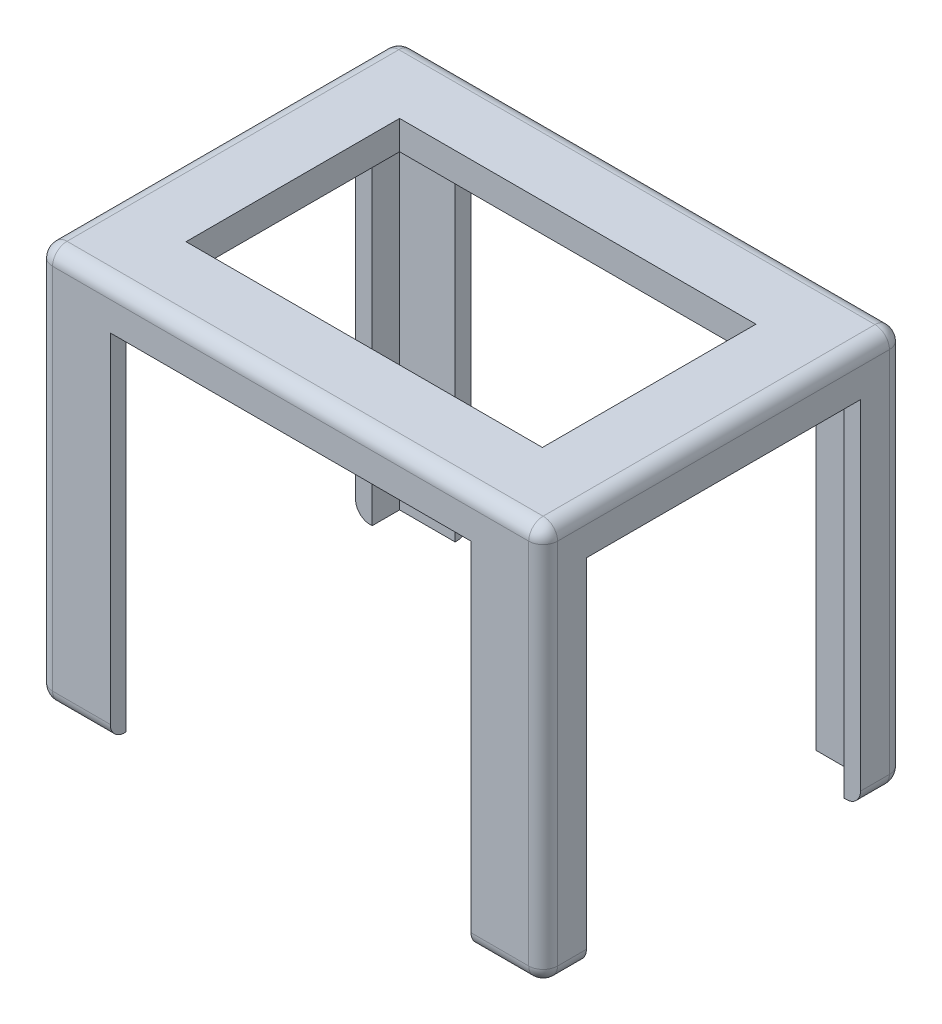
SolidWorks part; units mm, degrees
ref_plane "Front Plane" through (0, 0, 0) normal (0, 0, 1) x (1, 0, 0)
ref_plane "Top Plane" through (0, 0, 0) normal (0, 1, 0) x (1, 0, 0)
ref_plane "Right Plane" through (0, 0, 0) normal (1, 0, 0) x (0, 0, -1)
sketch "Sketch1" plane through (0, 0, 0) normal (0, 1, 0) x (1, 0, 0)
  line L1 (0, 0) -> (88.9, 0)
  line L2 (0, 0) -> (0, -63.5)
  line L3 (0, -63.5) -> (88.9, -63.5)
  line L4 (88.9, 0) -> (88.9, -63.5)
  dimension "D1" = 88.9
  dimension "D2" = 63.5
extrude "Boss-Extrude2" add sketch "Sketch1" along normal blind 69.85
fillet "Fillet2" radius 2.54 12 edges at (0, 69.85, 31.75) (0, 0, 31.75) (44.45, 69.85, 0) (0, 34.925, 0) (44.45, 0, 0) (88.9, 69.85, 31.75) (88.9, 34.925, 0) (88.9, 0, 31.75) (0, 34.925, 63.5) (44.45, 69.85, 63.5) (88.9, 34.925, 63.5) (44.45, 0, 63.5)
sketch "Sketch3" plane through (0, 69.85, 0) normal (0, 1, 0) x (1, 0, 0)
  line L0 (0, -2.54) -> (0, -60.96) construction
  line L1 (2.921, -2.794) -> (85.979, -2.794)
  line L2 (2.921, -2.794) -> (2.921, -60.706)
  line L3 (2.921, -60.706) -> (85.979, -60.706)
  line L4 (85.979, -2.794) -> (85.979, -60.706)
  line L5 (2.54, 0) -> (86.36, 0) construction
  point P6 (44.45, -60.706)
  dimension "D1" = 2.921
  dimension "D2" = 83.058
  dimension "D3" = 57.912
  dimension "D4" = 2.794
extrude "Cut-Extrude1" cut sketch "Sketch3" against normal through all from offset 5.08 offset against normal yes
sketch "Sketch5" plane through (0, 0, 63.5) normal (0, 0, 1) x (1, 0, 0)
  line L0 (2.54, 67.31) -> (2.54, 2.54) construction
  line L1 (76.2, 62.23) -> (12.7, 62.23)
  line L2 (76.2, 62.23) -> (76.2, -13.97)
  line L3 (76.2, -13.97) -> (12.7, -13.97)
  line L4 (12.7, 62.23) -> (12.7, -13.97)
  line L5 (86.36, 2.54) -> (86.36, 67.31) construction
  line L6 (86.36, 67.31) -> (2.54, 67.31) construction
  dimension "D1" = 10.16
  dimension "D2" = 10.16
  dimension "D3" = 5.08
  dimension "D4" = 76.2
extrude "Cut-Extrude3" cut sketch "Sketch5" against normal through all both and the other way through all
sketch "Sketch6" plane through (0, 0, 0) normal (-1, 0, 0) x (0, 0, 1)
  line L0 (60.96, 2.54) -> (60.96, 67.31) construction
  line L1 (55.88, 62.23) -> (7.62, 62.23)
  line L2 (55.88, 62.23) -> (55.88, -13.97)
  line L3 (55.88, -13.97) -> (7.62, -13.97)
  line L4 (7.62, 62.23) -> (7.62, -13.97)
  line L5 (2.54, 67.31) -> (2.54, 2.54) construction
  line L6 (60.96, 67.31) -> (2.54, 67.31) construction
  dimension "D1" = 5.08
  dimension "D2" = 5.08
  dimension "D3" = 5.08
  dimension "D4" = 76.2
extrude "Cut-Extrude4" cut sketch "Sketch6" against normal through all both and the other way through all
sketch "Sketch7" plane through (0, 64.77, 0) normal (0, -1, 0) x (1, 0, 0)
  line L0 (12.7, 2.794) -> (76.2, 2.794) construction
  line L1 (75.819, 12.954) -> (13.081, 12.954)
  line L2 (75.819, 12.954) -> (75.819, 50.546)
  line L3 (75.819, 50.546) -> (13.081, 50.546)
  line L4 (13.081, 12.954) -> (13.081, 50.546)
  line L5 (76.2, 60.706) -> (12.7, 60.706) construction
  line L6 (85.979, 60.706) -> (85.979, 2.794) construction
  line L7 (2.921, 55.88) -> (2.921, 7.62) construction
  dimension "D1" = 10.16
  dimension "D2" = 10.16
  dimension "D3" = 10.16
  dimension "D4" = 10.16
extrude "Cut-Extrude5" cut sketch "Sketch7" against normal through all
